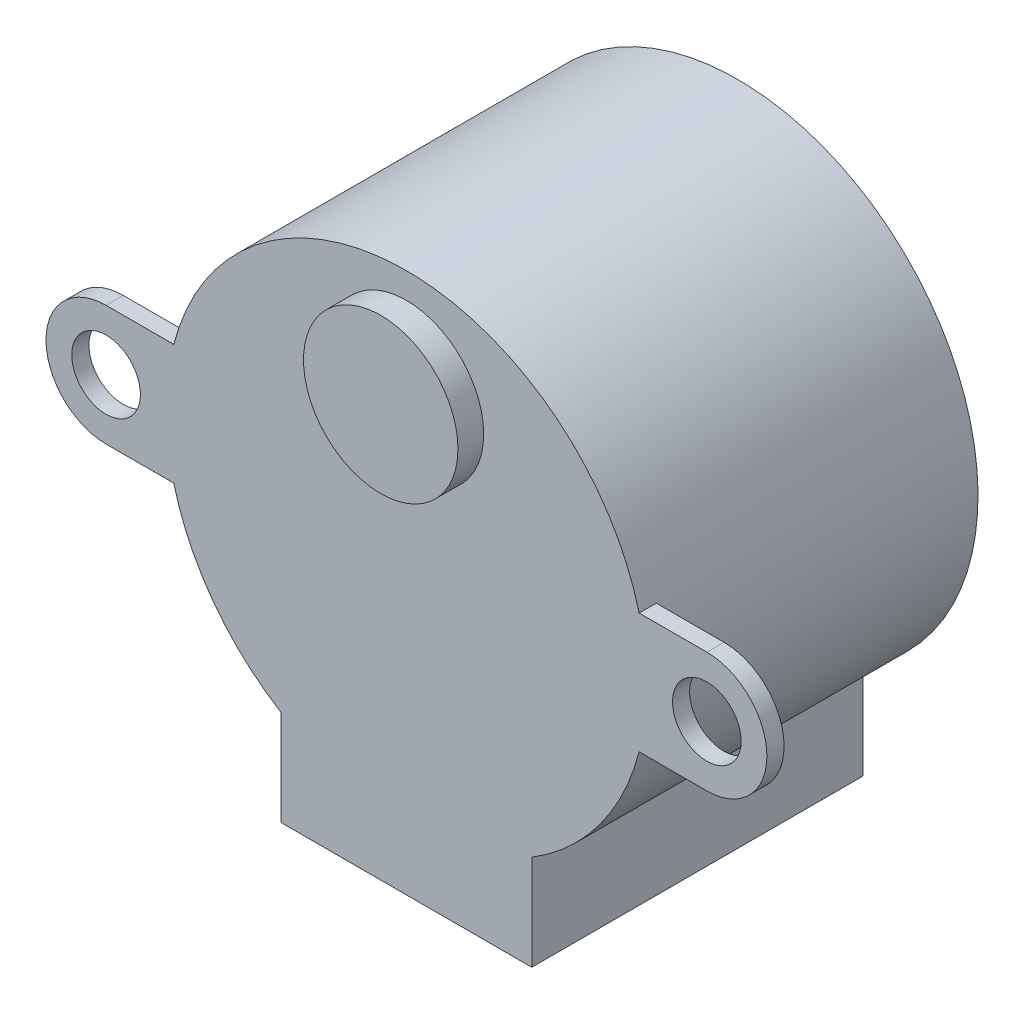
SolidWorks part; units mm, degrees
ref_plane "前视基准面" through (0, 0, 0) normal (0, 0, 1) x (1, 0, 0)
ref_plane "上视基准面" through (0, 0, 0) normal (0, 1, 0) x (1, 0, 0)
ref_plane "右视基准面" through (0, 0, 0) normal (1, 0, 0) x (0, 0, -1)
other "Configuration Table"
sketch "草图1" plane through (0, 0, 0) normal (0, 0, 1) x (1, 0, 0)
  circle A0 centre (-50.0235, 38.5026) radius 14
  dimension "D1" = 28
extrude "凸台-拉伸1" add sketch "草图1" along normal blind 19.3
sketch "草图3" plane through (0, 0, 19.3) normal (0, 0, 1) x (1, 0, 0)
  line L0 (-67.5235, 38.5026) -> (-32.5235, 38.5026) construction
  line L1 (-67.5235, 42.0026) -> (-32.5235, 42.0026)
  line L2 (-67.5235, 35.0026) -> (-32.5235, 35.0026)
  line L3 (-57.3235, 21.0026) -> (-42.7235, 21.0026)
  line L4 (-50.0235, 21.0026) -> (-50.0235, 28.6146) construction
  line L5 (-42.7235, 21.0026) -> (-42.7235, 26.5565)
  line L6 (-57.3235, 21.0026) -> (-57.3235, 26.5565)
  arc A0 (-67.5235, 42.0026) -> (-67.5235, 35.0026) centre (-67.5235, 38.5026) ccw
  circle A1 centre (-50.0235, 38.5026) radius 14
  circle A2 centre (-50.0235, 38.5026) radius 14 construction
  arc A3 (-32.5235, 35.0026) -> (-32.5235, 42.0026) centre (-32.5235, 38.5026) ccw
  circle A4 centre (-32.5235, 38.5026) radius 2
  circle A5 centre (-67.5235, 38.5026) radius 2
  point P5 (-50.0235, 38.5026)
  circle M6 centre (-50.0235, 38.5026) radius 14
  dimension "D4" = 4
  dimension "D5" = 3.5
  dimension "D6" = 35
  dimension "D2" = 17.5
  dimension "D3" = 14.6
  dimension "D1" = 0
extrude "凸台-拉伸2" add sketch "草图3" against normal blind 1 contours L1 A0 L2 A5 M6 | L2 A3 L1 A4 M6 | L6 L3 L5 M6
sketch "草图4" plane through (0, 0, 19.3) normal (0, 0, 1) x (1, 0, 0)
  line L0 (-67.5235, 38.5026) -> (-32.5235, 38.5026) construction
  line L1 (-50.0235, 38.5026) -> (-50.0235, 50.3774) construction
  circle A0 centre (-32.5235, 38.5026) radius 2 construction
  circle A1 centre (-67.5235, 38.5026) radius 2 construction
  circle A2 centre (-32.5235, 38.5026) radius 2 construction
  circle A3 centre (-67.5235, 38.5026) radius 2 construction
  circle A4 centre (-50.0235, 46.5026) radius 4.5
  dimension "D2" = 9
  dimension "D1" = 8
extrude "凸台-拉伸3" add sketch "草图4" along normal blind 1.5
sketch "草图5" plane through (0, 0, 20.8) normal (0, 0, 1) x (1, 0, 0)
  circle A0 centre (-50.0235, 46.5026) radius 2.5
  dimension "D1" = 5
sketch "草图6" plane through (0, 0, 19.3) normal (0, 0, 1) x (1, 0, 0)
  line L1 (-57.3235, 21.0026) -> (-42.7235, 21.0026)
  line L2 (-57.3235, 21.0026) -> (-57.3235, 26.5565)
  line L3 (-57.3235, 26.5565) -> (-42.7235, 26.5565)
  line L4 (-42.7235, 21.0026) -> (-42.7235, 26.5565)
extrude "凸台-拉伸4" add sketch "草图6" against normal up to surface (19.3 mm away) up to face at (-36.0235, 38.5026, 0)
